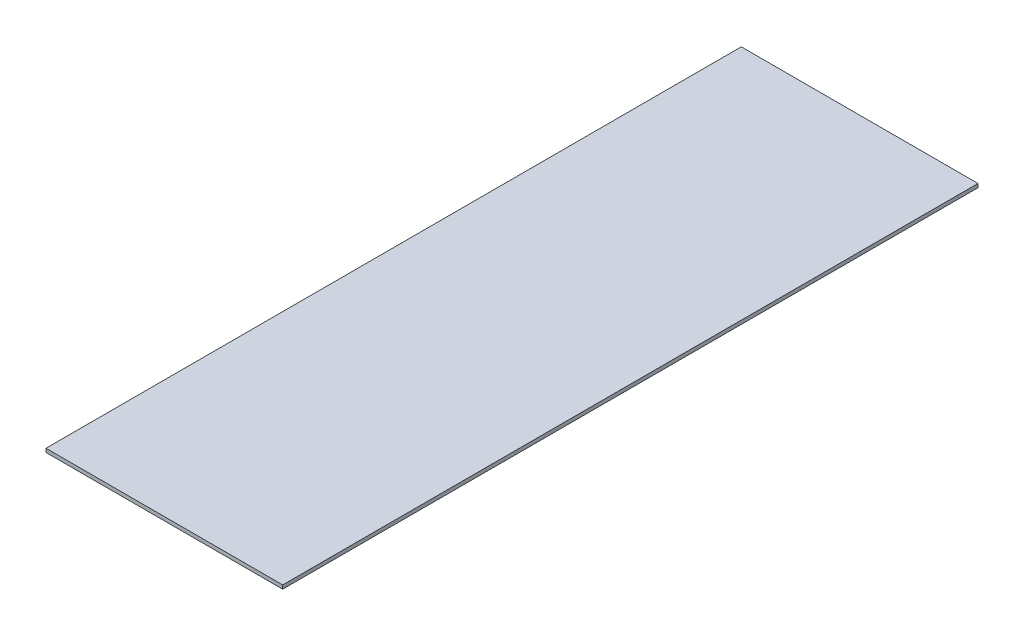
SolidWorks part; units mm, degrees
ref_plane "Front Plane" through (0, 0, 0) normal (0, 0, 1) x (1, 0, 0)
ref_plane "Top Plane" through (0, 0, 0) normal (0, 1, 0) x (1, 0, 0)
ref_plane "Right Plane" through (0, 0, 0) normal (1, 0, 0) x (0, 0, -1)
sketch "Sketch1" plane through (0, 0, 0) normal (0, 1, 0) x (1, 0, 0)
  line L1 (-25.4, 74.6125) -> (25.4, 74.6125)
  line L2 (-25.4, 74.6125) -> (-25.4, -74.6125)
  line L3 (-25.4, -74.6125) -> (25.4, -74.6125)
  line L4 (25.4, 74.6125) -> (25.4, -74.6125)
  line L5 (-25.4, 74.6125) -> (25.4, -74.6125) construction
  line L6 (-25.4, -74.6125) -> (25.4, 74.6125) construction
  point P0 (0, 0)
  dimension "D1" = 50.8
  dimension "D2" = 149.225
sketch "Sketch2" plane through (0, 0, 0) normal (0, 1, 0) x (1, 0, 0)
  line L4 (25.4, 74.6125) -> (-25.4, 74.6125)
  line L5 (25.4, -74.6125) -> (25.4, 74.6125)
  line L6 (-25.4, -74.6125) -> (25.4, -74.6125)
  line L7 (-25.4, 74.6125) -> (-25.4, -74.6125)
  line L8 (25.4, 74.6125) -> (-25.4, 74.6125)
  line L9 (25.4, -74.6125) -> (25.4, 74.6125)
  line L10 (-25.4, -74.6125) -> (25.4, -74.6125)
  line L11 (-25.4, 74.6125) -> (-25.4, -74.6125)
  dimension "D1" = 0
extrude "Boss-Extrude1" add sketch "Sketch2" along normal blind 0.7937
sketch "Sketch3" [suppressed] plane through (0, 0, 0) normal (0, 1, 0) x (1, 0, 0)
  line L4 (25.4, 74.6125) -> (-25.4, 74.6125)
  line L5 (25.4, -74.6125) -> (25.4, 74.6125)
  line L6 (-25.4, -74.6125) -> (25.4, -74.6125)
  line L7 (-25.4, 74.6125) -> (-25.4, -74.6125)
  line L12 (25.4, 74.6125) -> (-25.4, 74.6125)
  line L13 (25.4, -74.6125) -> (25.4, 74.6125)
  line L14 (-25.4, -74.6125) -> (25.4, -74.6125)
  line L15 (-25.4, 74.6125) -> (-25.4, -74.6125)
  dimension "D1" = 0
extrude "Boss-Extrude2" [suppressed] add sketch "Sketch3" along normal blind 0.7937
